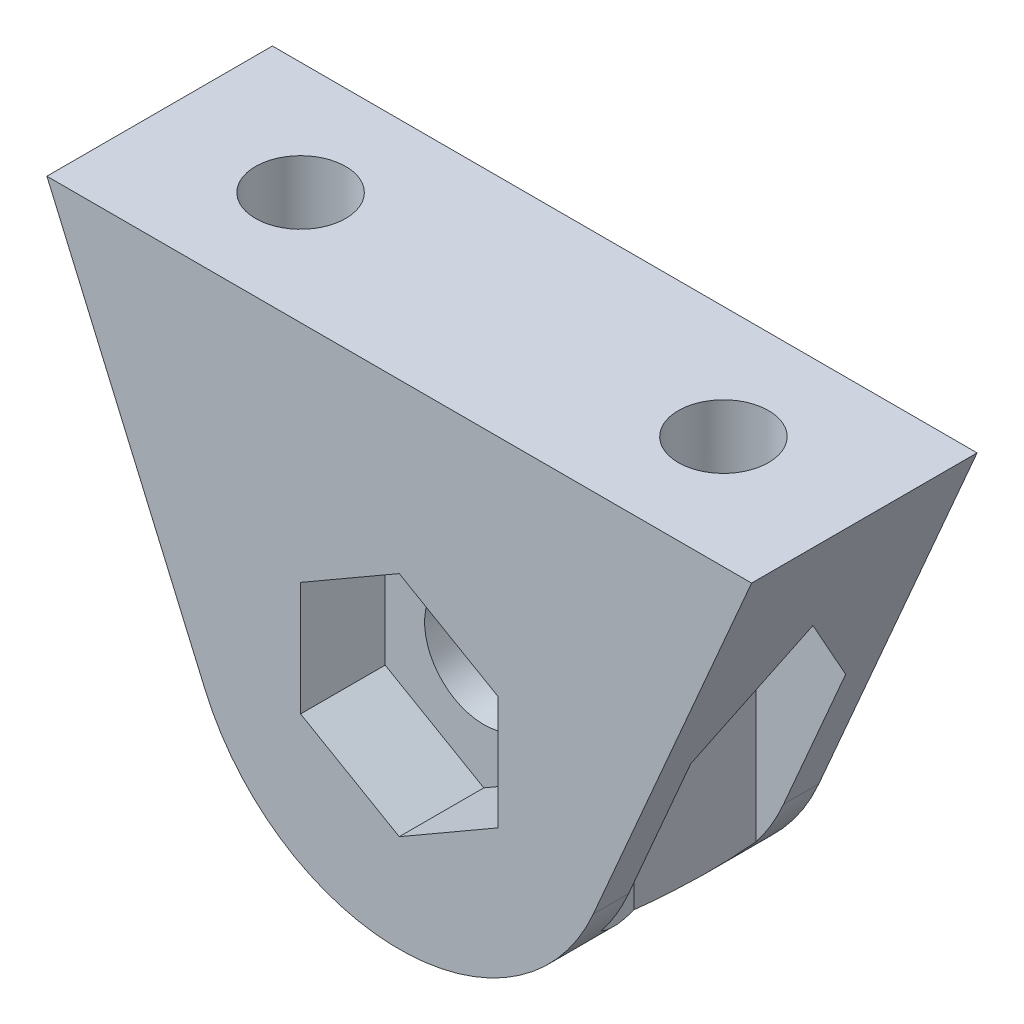
SolidWorks part; units mm, degrees
ref_plane "Front Plane" through (0, 0, 0) normal (0, 0, 1) x (1, 0, 0)
ref_plane "Top Plane" through (0, 0, 0) normal (0, 1, 0) x (1, 0, 0)
ref_plane "Right Plane" through (0, 0, 0) normal (1, 0, 0) x (0, 0, -1)
sketch "Sketch1" plane through (0, 0, 0) normal (0, 0, 1) x (1, 0, 0)
  line L0 (-6.8831, -2.9788) -> (-12.5, 10)
  line L1 (-12.5, 10) -> (12.5, 10)
  line L2 (0, 0) -> (0, 10) construction
  line L3 (6.8831, -2.9788) -> (12.5, 10)
  arc A0 (-6.8831, -2.9788) -> (6.8831, -2.9788) centre (0, 0) ccw
  circle A1 centre (0, 0) radius 2.1
  dimension "D1" = 10
  dimension "D2" = 15
  dimension "D4" = 4.2
  dimension "D3" = 25
extrude "Boss-Extrude1" add sketch "Sketch1" along normal blind 8 contours L0 L1 L3 A0
sketch "Sketch2" plane through (0, 10, 0) normal (0, 1, 0) x (1, 0, 0)
  line L0 (-12.5, 0) -> (12.5, -8) construction
  line L1 (-7.5, -4) -> (7.5, -4) construction
  circle A0 centre (-7.5, -4) radius 1.6
  circle A1 centre (7.5, -4) radius 1.6
  point P7 (0, -4)
  dimension "D2" = 3.2
  dimension "D1" = 15
extrude "Cut-Extrude1" cut sketch "Sketch2" against normal through all
sketch "Sketch3" plane through (0, 0, 8) normal (0, 0, 1) x (1, 0, 0)
  line L1 (0, -4.0415) -> (3.5, -2.0207)
  line L2 (3.5, -2.0207) -> (3.5, 2.0207)
  line L3 (3.5, 2.0207) -> (0, 4.0415)
  line L4 (0, 4.0415) -> (-3.5, 2.0207)
  line L5 (-3.5, 2.0207) -> (-3.5, -2.0207)
  line L6 (-3.5, -2.0207) -> (0, -4.0415)
  circle A0 centre (0, 0) radius 3.5 construction
  dimension "D1" = 7
extrude "Cut-Extrude2" cut sketch "Sketch3" against normal blind 3
sketch "Sketch4" plane through (0, 10, 0) normal (0, 1, 0) x (1, 0, 0)
  line L0 (0, 0) -> (0, -8) construction
  line L1 (-5.9123, -6.75) -> (-4.3246, -4)
  line L2 (-4.3246, -4) -> (-5.9123, -1.25)
  line L3 (-5.9123, -1.25) -> (-9.0877, -1.25)
  line L4 (-9.0877, -1.25) -> (-10.6754, -4)
  line L5 (-10.6754, -4) -> (-9.0877, -6.75)
  line L6 (-9.0877, -6.75) -> (-5.9123, -6.75)
  line L7 (12.5, 0) -> (-12.5, 0) construction
  line L8 (12.5, -8) -> (-12.5, -8) construction
  line L9 (9.0877, -6.75) -> (5.9123, -6.75)
  line L10 (10.6754, -4) -> (9.0877, -6.75)
  line L11 (9.0877, -1.25) -> (10.6754, -4)
  line L12 (5.9123, -1.25) -> (9.0877, -1.25)
  line L13 (4.3246, -4) -> (5.9123, -1.25)
  line L14 (5.9123, -6.75) -> (4.3246, -4)
  circle A0 centre (-7.5, -4) radius 2.75 construction
  circle A1 centre (7.5, -4) radius 2.75 construction
  dimension "D1" = 5.5
extrude "Cut-Extrude3" cut sketch "Sketch4" against normal through all from offset 3
